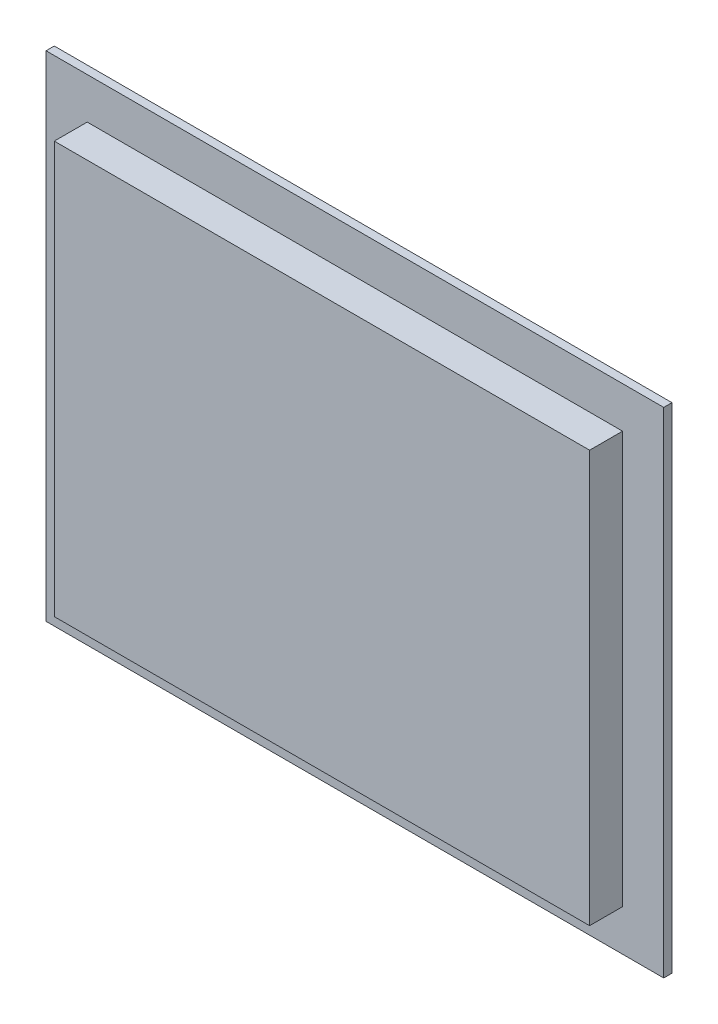
SolidWorks part; units mm, degrees
ref_plane "Front Plane" through (0, 0, 0) normal (0, 0, 1) x (1, 0, 0)
ref_plane "Top Plane" through (0, 0, 0) normal (0, 1, 0) x (1, 0, 0)
ref_plane "Right Plane" through (0, 0, 0) normal (1, 0, 0) x (0, 0, -1)
sketch "Sketch1" plane through (0, 0, 0) normal (0, 0, 1) x (1, 0, 0)
  line L0 (-130, 100) -> (130, 100)
  line L1 (-150, -120) -> (150, -120)
  line L2 (-150, -120) -> (-150, 120)
  line L3 (-150, 120) -> (150, 120)
  line L4 (150, -120) -> (150, 120)
  line L5 (-150, -120) -> (150, 120) construction
  line L6 (-150, 120) -> (150, -120) construction
  line L7 (130, -100) -> (130, 100)
  line L8 (-130, -100) -> (130, -100)
  line L9 (-130, -100) -> (-130, 100)
  point P0 (0, 0)
  dimension "D1" = 300
  dimension "D2" = 240
  dimension "D3" = 20
extrude "Boss-Extrude1" add sketch "Sketch1" along normal blind 4
sketch "Sketch2" plane through (0, 0, 4) normal (0, 0, 1) x (1, 0, 0)
  line L1 (-130, -100) -> (130, -100)
  line L2 (-130, -100) -> (-130, 100)
  line L3 (-130, 100) -> (130, 100)
  line L4 (130, -100) -> (130, 100)
  line L5 (-130, -100) -> (130, 100) construction
  line L6 (-130, 100) -> (130, -100) construction
  line L7 (-126.1, -97) -> (126.1, -97)
  line L8 (-126.1, -97) -> (-126.1, 97)
  line L9 (-126.1, 97) -> (126.1, 97)
  line L10 (126.1, -97) -> (126.1, 97)
  line L11 (-126.1, -97) -> (126.1, 97) construction
  line L12 (-126.1, 97) -> (126.1, -97) construction
  point P0 (0, 0)
  point P5 (0, 0)
  dimension "D1" = 3
extrude "Boss-Extrude3" add sketch "Sketch2" along normal blind 16 and the other way through all
sketch "Sketch4" plane through (0, 0, 20) normal (0, 0, 1) x (1, 0, 0)
  line L1 (-126.1, -97) -> (126.1, -97)
  line L2 (-126.1, -97) -> (-126.1, 97)
  line L3 (-126.1, 97) -> (126.1, 97)
  line L4 (126.1, -97) -> (126.1, 97)
  line L5 (-126.1, -97) -> (126.1, 97) construction
  line L6 (-126.1, 97) -> (126.1, -97) construction
  point P0 (0, 0)
extrude "Boss-Extrude4" add sketch "Sketch4" against normal blind 4
